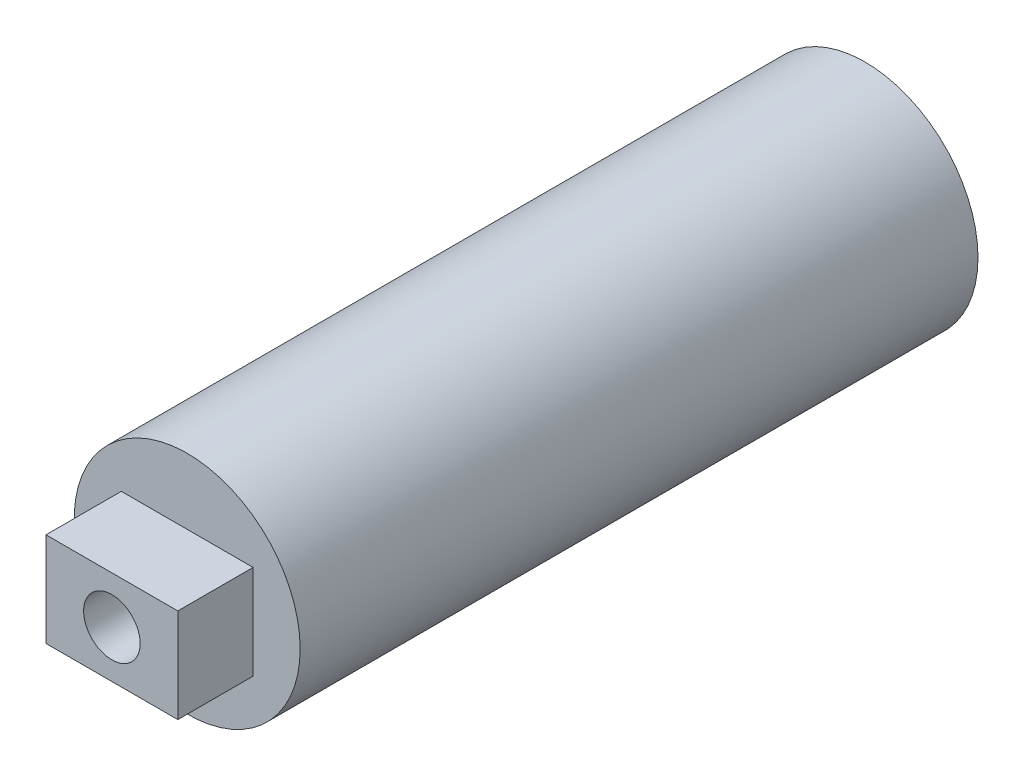
SolidWorks part; units mm, degrees
ref_plane "Front Plane" through (0, 0, 0) normal (0, 0, 1) x (1, 0, 0)
ref_plane "Top Plane" through (0, 0, 0) normal (0, 1, 0) x (1, 0, 0)
ref_plane "Right Plane" through (0, 0, 0) normal (1, 0, 0) x (0, 0, -1)
sketch "Sketch9" plane through (0, 0, 0) normal (0, 0, 1) x (1, 0, 0)
  circle A0 centre (0, 0) radius 30
extrude "Boss-Extrude11" add sketch "Sketch9" along normal blind 180
sketch "Sketch10" plane through (0, 0, 180) normal (0, 0, 1) x (1, 0, 0)
  line L1 (-17.5, 12.5) -> (17.5, 12.5)
  line L2 (-17.5, 12.5) -> (-17.5, -12.5)
  line L3 (-17.5, -12.5) -> (17.5, -12.5)
  line L4 (17.5, 12.5) -> (17.5, -12.5)
  line L5 (-17.5, 12.5) -> (17.5, -12.5) construction
  line L6 (-17.5, -12.5) -> (17.5, 12.5) construction
  point P0 (0, 0)
extrude "Boss-Extrude12" add sketch "Sketch10" along normal blind 20
sketch "Sketch11" plane through (0, 0, 200) normal (0, 0, 1) x (1, 0, 0)
  circle A0 centre (0, 0) radius 7.5
extrude "Cut-Extrude2" cut sketch "Sketch11" against normal through all
shell "Shell1" thickness 1
